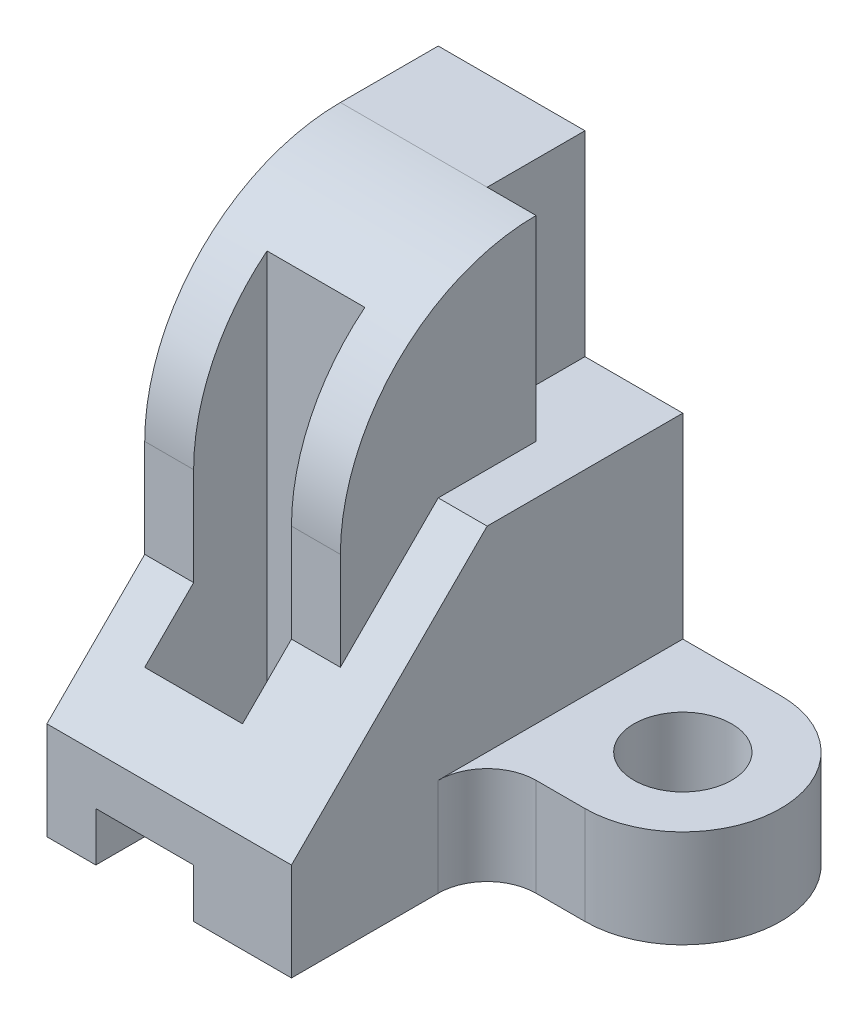
SolidWorks part; units mm, degrees
ref_plane "Front Plane" through (0, 0, 0) normal (0, 0, 1) x (1, 0, 0)
ref_plane "Top Plane" through (0, 0, 0) normal (0, 1, 0) x (1, 0, 0)
ref_plane "Right Plane" through (0, 0, 0) normal (1, 0, 0) x (0, 0, -1)
sketch "Sketch1" plane through (0, 0, 0) normal (0, 0, 1) x (1, 0, 0)
  line L0 (0, 0) -> (-2, 0)
  line L1 (-2, 0) -> (-2, 1)
  line L2 (-2, 1) -> (-4, 1)
  line L3 (-4, 1) -> (-4, 0)
  line L4 (-4, 0) -> (-5, 0)
  line L5 (-5, 0) -> (-5, 10)
  line L6 (-5, 10) -> (-1, 10)
  line L7 (-1, 10) -> (-1, 6)
  line L8 (-1, 6) -> (0, 6)
  line L9 (0, 6) -> (0, 0)
  dimension "D1" = 2
  dimension "D2" = 1
  dimension "D3" = 2
  dimension "D4" = 10
  dimension "D5" = 4
  dimension "D6" = 6
  dimension "D7" = 1
extrude "Boss-Extrude2" add sketch "Sketch1" along normal blind 8
sketch "Sketch2" plane through (0, 0, 0) normal (0, -1, 0) x (1, 0, 0)
  line L0 (0, 8) -> (0, 0) construction
  line L1 (-2, 0) -> (0, 0) construction
  line L2 (0, 0) -> (2, 0)
  line L3 (1, 4) -> (2, 4)
  line L4 (0, 5) -> (0, 0)
  circle A0 centre (2, 2) radius 1
  arc A1 (1, 4) -> (0, 5) centre (1, 5) cw
  arc A2 (2, 4) -> (2, 0) centre (2, 2) cw
  dimension "D3" = 2
  dimension "D1" = 2
  dimension "D2" = 2
  dimension "D4" = 2
  dimension "D5" = 3
  dimension "D6" = 1
  dimension "D7" = 1
  dimension "D8" = 1
extrude "Boss-Extrude3" add sketch "Sketch2" against normal blind 2
sketch "Sketch3" plane through (0, 10, 0) normal (0, 1, 0) x (1, 0, 0)
  line L0 (-2, 0) -> (-2, -2)
  line L1 (-1, 0) -> (-5, 0) construction
  line L2 (-2, -2) -> (-1, -2)
  line L3 (-1, -8) -> (-1, 0) construction
  line L4 (-1, -2) -> (-1, -8)
  line L5 (-1, -8) -> (0, -8)
  line L6 (0, -8) -> (0, 0)
  line L7 (0, 0) -> (-2, 0)
  dimension "D1" = 2
  dimension "D2" = 2
extrude "Cut-Extrude1" cut sketch "Sketch3" against normal blind 4
sketch "Sketch4" plane through (-1, 0, 0) normal (1, 0, 0) x (0, 0, -1)
  line L3 (0, 2) -> (0, 6) construction
  line L4 (-2, 10) -> (-8, 10)
  line L5 (-8, 10) -> (-8, 2)
  line L6 (-8, 0) -> (-8, 6) construction
  line L7 (-6, 4) -> (-8, 2)
  line L8 (-6, 4) -> (-6, 6)
  arc A0 (-6, 6) -> (-2, 10) centre (-2, 6) cw
  dimension "D1" = 4
  dimension "D2" = 6
  dimension "D4" = 2
  dimension "D5" = 2
extrude "Cut-Extrude2" cut sketch "Sketch4" against normal mid plane 10
sketch "Sketch5" plane through (0, 0, 0) normal (1, 0, 0) x (0, 0, -1)
  line L0 (-4, 6) -> (-6, 4)
  line L1 (-6, 6) -> (0, 6) construction
  line L2 (-6, 4) -> (-6, 6)
  line L3 (-6, 6) -> (-4, 6)
  dimension "D1" = 4
extrude "Cut-Extrude3" cut sketch "Sketch5" against normal blind 1
sketch "Sketch6" plane through (0, 1, 0) normal (0, -1, 0) x (1, 0, 0)
  line L0 (-2, 7) -> (-4, 7)
  line L1 (-2, 8) -> (-2, 0) construction
  line L2 (-4, 8) -> (-4, 0) construction
  line L3 (-4, 7) -> (-4, 4.5)
  line L4 (-4, 4.5) -> (-2, 4.5)
  line L5 (-2, 8) -> (-2, 0) construction
  line L6 (-2, 4.5) -> (-2, 7)
  dimension "D1" = 1
  dimension "D2" = 2.5
extrude "Cut-Extrude4" cut sketch "Sketch6" against normal through all
